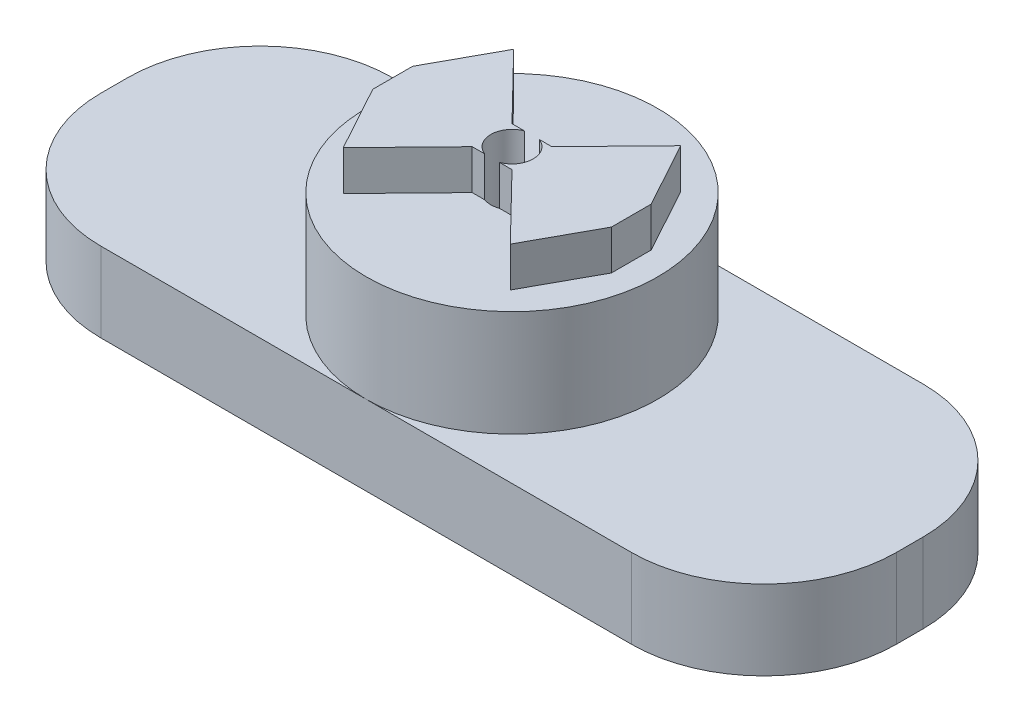
SolidWorks part; units mm, degrees
ref_plane "Płaszczyzna przednia" through (0, 0, 0) normal (0, 0, 1) x (1, 0, 0)
ref_plane "Płaszczyzna górna" through (0, 0, 0) normal (0, 1, 0) x (1, 0, 0)
ref_plane "Płaszczyzna prawa" through (0, 0, 0) normal (1, 0, 0) x (0, 0, -1)
sketch "Sketch1" plane through (0, 0, 0) normal (0, 1, 0) x (1, 0, 0)
  line L5 (-20.01, -11) -> (20.01, -11)
  line L6 (-30, -1.01) -> (-30, 1.01)
  line L7 (-20.01, 11) -> (20.01, 11)
  line L8 (30, -1.01) -> (30, 1.01)
  line L9 (-30, -11) -> (30, 11) construction
  line L10 (-30, 11) -> (30, -11) construction
  arc A0 (-20.01, -11) -> (-30, -1.01) centre (-20.01, -1.01) cw
  arc A1 (20.01, -11) -> (30, -1.01) centre (20.01, -1.01) ccw
  arc A2 (20.01, 11) -> (30, 1.01) centre (20.01, 1.01) cw
  arc A3 (-30, 1.01) -> (-20.01, 11) centre (-20.01, 1.01) cw
  point P0 (0, 0)
  point P1 (0, 0)
  dimension "D3" = 9.99
  dimension "D1" = 60
  dimension "D2" = 22
extrude "Boss-Extrude1" add sketch "Sketch1" along normal blind 6
sketch "Sketch2" plane through (0, 6, 0) normal (0, 1, 0) x (1, 0, 0)
  line L0 (0, 0) -> (-3, 0) construction
  line L1 (0, 0) -> (3, 0) construction
  circle A3 centre (0, 0) radius 11
extrude "Boss-Extrude2" add sketch "Sketch2" along normal blind 8
sketch "Sketch12" plane through (0, 0, 0) normal (0, -1, 0) x (1, 0, 0)
  circle A0 centre (0, 0) radius 6
extrude "Cut-Extrude2" cut sketch "Sketch12" against normal blind 4
sketch "Sketch18" plane through (0, 4, 0) normal (0, -1, 0) x (-1, 0, 0)
  point P0 (0, 0)
sketch "Sketch19" plane through (0, 14, 0) normal (0, 1, 0) x (1, 0, 0)
  line L26 (-6.3004, 6.4269) -> (-9, 1.5)
  line L27 (-1.5, -1.5) -> (1.5, -1.5) construction
  line L28 (-1.5, -1.5) -> (-1.5, 1.5) construction
  line L29 (-1.5, 1.5) -> (1.5, 1.5) construction
  line L30 (1.5, -1.5) -> (1.5, 1.5) construction
  line L31 (-1.5, -1.5) -> (1.5, 1.5) construction
  line L32 (-1.5, 1.5) -> (1.5, -1.5) construction
  line L33 (-6.3004, -6.4269) -> (6.3004, -6.4269) construction
  line L34 (-6.3004, -6.4269) -> (-6.3004, 6.4269) construction
  line L35 (-6.3004, 6.4269) -> (6.3004, 6.4269) construction
  line L36 (6.3004, -6.4269) -> (6.3004, 6.4269) construction
  line L37 (-6.3004, -6.4269) -> (6.3004, 6.4269) construction
  line L38 (-6.3004, 6.4269) -> (6.3004, -6.4269) construction
  line L39 (-9, -1.5) -> (9, -1.5) construction
  line L40 (-9, -1.5) -> (-9, 1.5) construction
  line L41 (-9, 1.5) -> (9, 1.5) construction
  line L42 (9, -1.5) -> (9, 1.5) construction
  line L43 (-9, -1.5) -> (9, 1.5) construction
  line L44 (-9, 1.5) -> (9, -1.5) construction
  line L45 (-9, 1.5) -> (-9, -1.5)
  line L46 (-9, -1.5) -> (-6.3004, -6.4269)
  line L47 (-6.3004, -6.4269) -> (-1.5, -1.5)
  line L48 (-1.5, -1.5) -> (1.5, -1.5)
  line L49 (1.5, -1.5) -> (6.3004, -6.4269)
  line L50 (6.3004, -6.4269) -> (9, -1.5)
  line L51 (9, -1.5) -> (9, 1.5)
  line L52 (9, 1.5) -> (6.3004, 6.4269)
  line L53 (6.3004, 6.4269) -> (1.5, 1.5)
  line L54 (1.5, 1.5) -> (-1.5, 1.5)
  line L55 (-1.5, 1.5) -> (-6.3004, 6.4269)
  point P16 (0, 0)
  point P22 (0, 0)
  point P27 (0, 0)
  dimension "D1" = 12.6008
  dimension "D2" = 12.8538
  dimension "D4" = 3
  dimension "D5" = 3
  dimension "D6" = 18
  dimension "D7" = 18
extrude "Boss-Extrude3" add sketch "Sketch19" along normal blind 3
hole_wizard "CSK for M3 Countersunk Flat Head Screw3" positions "Sketch18" profile "Sketch17" countersink size "M3" standard "ISO" end condition through all
sketch "Sketch17" plane through (0, 4, 0) normal (1, 0, 0) x (0, 0, -1)
  line L0 (0, 0) -> (0, 13)
  line L1 (0, 13) -> (1.6, 13)
  line L2 (1.6, 13) -> (1.6, 1.55)
  line L3 (1.6, 1.55) -> (3.15, 0)
  line L5 (3.15, 0) -> (0, 0)
  line L6 (-1.6, 1.55) -> (-3.15, 0) construction
  line L11 (0, -6.35) -> (0, 107.95) construction
  dimension "Thru Hole Dia." = 3.2
  dimension "Thru Hole Depth" = 13
  dimension "Near C'Sink Dia." = 6.3
  dimension "Near C'Sink Angle" = 90
sketch "Sketch20" plane through (0, 0, 0) normal (0, -1, 0) x (1, 0, 0)
  line L0 (0, 0) -> (30, 0) construction
  line L1 (30, 1.01) -> (30, -1.01) construction
  line L2 (10, 0) -> (10, -2.5) construction
  line L3 (10, 0) -> (10, 2.5) construction
  line L4 (10, 2.5) -> (10, -2.5)
  line L5 (10, 2.5) -> (20, 2.5)
  line L6 (10, -2.5) -> (20, -2.5)
  line L8 (20, 2.5) -> (20, 6)
  line L9 (20, -2.5) -> (20, -6)
  line L10 (20, 6) -> (26, 0)
  line L11 (26, 0) -> (20, -6)
  point P5 (20, 0)
  point P6 (10, 0)
  point P7 (26, 0)
  point P8 (6, 0)
  dimension "D1" = 4
  dimension "D2" = 6
  dimension "D3" = 10
  dimension "D4" = 4
  dimension "D5" = 10
extrude "Cut-Extrude3" cut sketch "Sketch20" against normal blind 1
